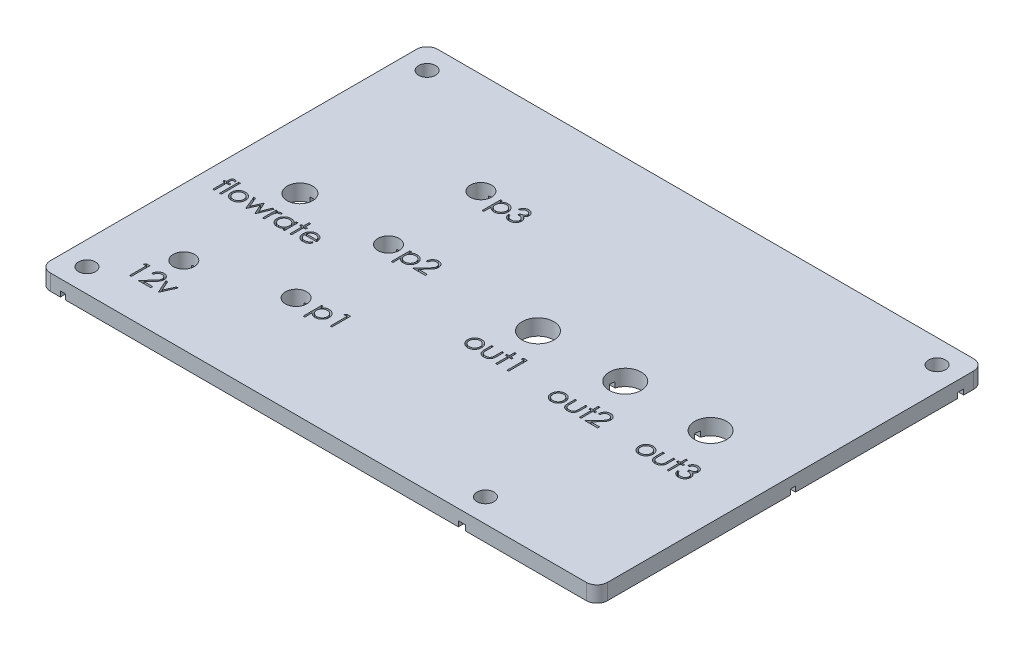
SolidWorks part; units mm, degrees
ref_plane "Front Plane" through (0, 0, 0) normal (0, 0, 1) x (1, 0, 0)
ref_plane "Top Plane" through (0, 0, 0) normal (0, 1, 0) x (1, 0, 0)
ref_plane "Right Plane" through (0, 0, 0) normal (1, 0, 0) x (0, 0, -1)
sketch "Sketch1" plane through (0, 0, 0) normal (0, 1, 0) x (1, 0, 0)
  line L1 (-52.5, 36.5) -> (52.5, 36.5)
  line L2 (-52.5, 36.5) -> (-52.5, -36.5)
  line L3 (-52.5, -36.5) -> (52.5, -36.5)
  line L4 (52.5, 36.5) -> (52.5, -36.5)
  line L5 (-52.5, 36.5) -> (52.5, -36.5) construction
  line L6 (-52.5, -36.5) -> (52.5, 36.5) construction
  point P0 (0, 0)
  dimension "D1" = 105
  dimension "D2" = 73
extrude "Boss-Extrude1" add sketch "Sketch1" along normal blind 3
sketch "Sketch2" plane through (0, 3, 0) normal (0, 1, 0) x (1, 0, 0)
  line L1 (-52.5, -36.5) -> (52.5, -36.5) construction
  line L2 (52.5, -36.5) -> (52.5, 36.5) construction
  line L5 (0, -55) -> (0, 55) construction
  line L6 (-52.5, 36.5) -> (-52.5, -36.5) construction
  line L7 (52.5, 36.5) -> (-52.5, 36.5) construction
  line L8 (-55, 0) -> (55, 0) construction
  circle A2 centre (48.05, 32.05) radius 1.6
  circle A3 centre (-48.05, 32.05) radius 1.6
  circle A4 centre (27.05, -32.05) radius 1.6
  circle A5 centre (-48.05, -32.05) radius 1.6
  dimension "D1" = 4.45
  dimension "D6" = 25.45
  dimension "D2" = 4.45
  dimension "D7" = 4.45
extrude "Cut-Extrude1" cut sketch "Sketch2" against normal blind 4
sketch "Sketch3" plane through (0, 3, 0) normal (0, 1, 0) x (1, 0, 0)
  line L0 (-55, 0) -> (55, 0) construction
  circle A0 centre (-39.9668, -21.888) radius 2
  circle A1 centre (-39.9668, 0) radius 2.4004
  circle A2 centre (-23.2787, 0) radius 2
  circle A3 centre (-23.2787, 17.4137) radius 2
  circle A4 centre (-23.2787, -17.4137) radius 2
  circle A5 centre (4.8976, 0) radius 3
  circle A6 centre (21.3438, 0) radius 3
  circle A7 centre (37.4273, 0) radius 3
extrude "Cut-Extrude2" cut sketch "Sketch3" against normal blind 4
sketch "Sketch4" plane through (0, 3, 0) normal (0, 1, 0) x (1, 0, 0)
  text T0 "12v"
  text T1 "p1\r\n"
  text T2 "p2"
  text T3 "p3\r\n"
  text T4 "out1\r\n"
  text T5 "out2"
  text T6 "out3"
  text T7 "flowrate"
  point P4 (-43.8274, -6.5864)
  point P5 (1.9, -10.3505)
  point P6 (18.6295, -10.3505)
  point P7 (33.8255, -10.3505)
extrude "Cut-Extrude3" cut sketch "Sketch4" against normal blind 1.5
fillet "Fillet1" radius 2 4 edges at (-52.5, 1.5, -36.5) (52.5, 1.5, -36.5) (52.5, 1.5, 36.5) (-52.5, 1.5, 36.5)
sketch "Sketch5" plane through (0, 0, 0) normal (0, -1, 0) x (1, 0, 0)
  line L0 (-50.5, 36.5) -> (50.5, 36.5) construction
  line L1 (-48.6123, 36.5) -> (-47.6123, 36.5)
  line L2 (-48.6123, 36.5) -> (-48.6123, -36.5)
  line L3 (-48.6123, -36.5) -> (-47.6123, -36.5)
  line L4 (-47.6123, 36.5) -> (-47.6123, -36.5)
  line L5 (50.5, -36.5) -> (-50.5, -36.5) construction
  line L6 (-40.4628, 36.4426) -> (-39.4628, 36.4426)
  line L7 (-40.4628, 36.4426) -> (-40.4628, -36.5574)
  line L8 (-40.4628, -36.5574) -> (-39.4628, -36.5574)
  line L9 (-39.4628, 36.4426) -> (-39.4628, -36.5574)
  line L10 (-23.7552, 36.3852) -> (-22.7552, 36.3852)
  line L11 (-23.7552, 36.3852) -> (-23.7552, -36.6148)
  line L12 (-23.7552, -36.6148) -> (-22.7552, -36.6148)
  line L13 (-22.7552, 36.3852) -> (-22.7552, -36.6148)
  line L14 (52.5, 34.5) -> (52.5, -34.5) construction
  line L15 (26.3855, 36.5) -> (27.7062, 36.5)
  line L16 (26.3855, 36.5) -> (26.3855, 32.3013)
  line L17 (26.3855, 32.3013) -> (27.7062, 32.3013)
  line L18 (27.7062, 36.5) -> (27.7062, 32.3013)
  line L19 (52.5, 0) -> (4.0438, 0)
  line L20 (52.5, 0) -> (52.5, -0.9362)
  line L21 (52.5, -0.9362) -> (4.0438, -0.9362)
  line L22 (4.0438, 0) -> (4.0438, -0.9362)
  line L24 (52.5, -31.4222) -> (47.4066, -31.4222)
  line L25 (52.5, -31.4222) -> (52.5, -32.6329)
  line L26 (52.5, -32.6329) -> (47.4066, -32.6329)
  line L27 (47.4066, -31.4222) -> (47.4066, -32.6329)
  dimension "D1" = 1
extrude "Cut-Extrude4" cut sketch "Sketch5" against normal blind 1
